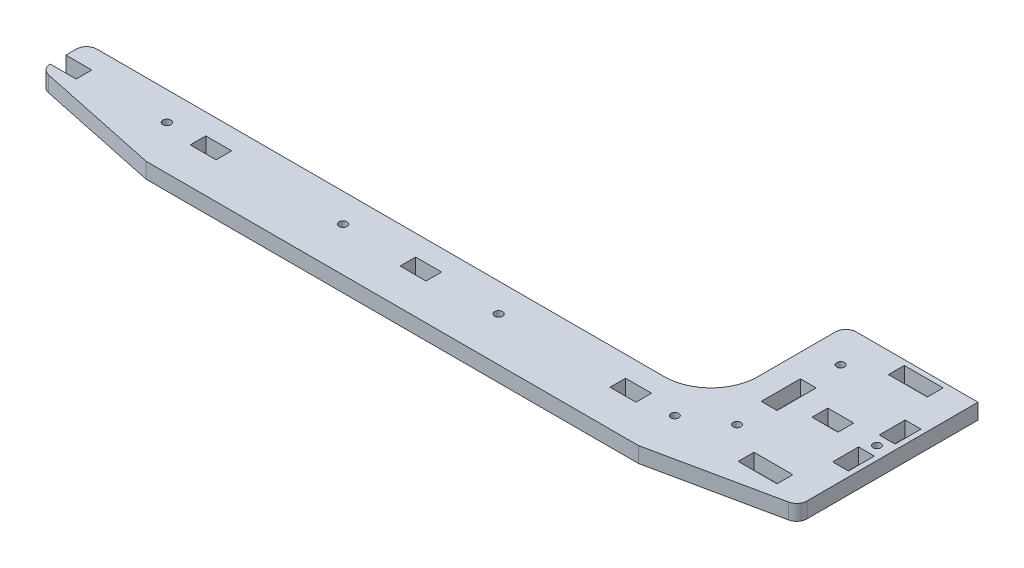
SolidWorks part; units mm, degrees
ref_plane "Спереди" through (0, 0, 0) normal (0, 0, 1) x (1, 0, 0)
ref_plane "Сверху" through (0, 0, 0) normal (0, 1, 0) x (1, 0, 0)
ref_plane "Справа" through (0, 0, 0) normal (1, 0, 0) x (0, 0, -1)
sketch "Эскиз1" plane through (0, 0, 0) normal (0, 1, 0) x (1, 0, 0)
  line L0 (105.2165, 20.9384) -> (111.3165, 20.9384)
  line L1 (111.3165, 20.9384) -> (111.3165, 30.9384)
  line L2 (111.3165, 30.9384) -> (105.2165, 30.9384)
  line L3 (105.2165, 30.9384) -> (105.2165, 20.9384)
  line L4 (71.2165, 9.3884) -> (77.3165, 9.3884)
  line L5 (77.3165, 9.3884) -> (77.3165, 24.4884)
  line L6 (77.3165, 24.4884) -> (71.2165, 24.4884)
  line L7 (71.2165, 24.4884) -> (71.2165, 9.3884)
  line L8 (96.3165, 19.9884) -> (86.3165, 19.9884)
  line L9 (86.3165, 19.9884) -> (86.3165, 13.8884)
  line L10 (86.3165, 13.8884) -> (96.3165, 13.8884)
  line L11 (96.3165, 13.8884) -> (96.3165, 19.9884)
  line L12 (111.3165, 2.9384) -> (111.3165, 12.9384)
  line L13 (111.3165, 12.9384) -> (105.2165, 12.9384)
  line L14 (105.2165, 12.9384) -> (105.2165, 2.9384)
  line L15 (105.2165, 2.9384) -> (111.3165, 2.9384)
  line L16 (101.8165, 48.9884) -> (86.8165, 48.9884)
  line L17 (86.8165, 48.9884) -> (86.8165, 42.8884)
  line L18 (86.8165, 42.8884) -> (101.8165, 42.8884)
  line L19 (101.8165, 42.8884) -> (101.8165, 48.9884)
  line L20 (86.8165, -15.1116) -> (101.8165, -15.1116)
  line L21 (101.8165, -15.1116) -> (101.8165, -9.0116)
  line L22 (101.8165, -9.0116) -> (86.8165, -9.0116)
  line L23 (86.8165, -9.0116) -> (86.8165, -15.1116)
  line L24 (-178.6835, -15.0616) -> (-168.6835, -15.0616)
  line L25 (-168.6835, -15.0616) -> (-168.6835, -9.0616)
  line L26 (-168.6835, -9.0616) -> (-178.6835, -9.0616)
  line L27 (-124.6835, -15.0616) -> (-114.6835, -15.0616)
  line L28 (-114.6835, -15.0616) -> (-114.6835, -9.0616)
  line L29 (-114.6835, -9.0616) -> (-124.6835, -9.0616)
  line L30 (-124.6835, -9.0616) -> (-124.6835, -15.0616)
  line L31 (-43.6835, -15.0616) -> (-33.6835, -15.0616)
  line L32 (-33.6835, -15.0616) -> (-33.6835, -9.0616)
  line L33 (-33.6835, -9.0616) -> (-43.6835, -9.0616)
  line L34 (-43.6835, -9.0616) -> (-43.6835, -15.0616)
  line L35 (37.3165, -15.0616) -> (47.3165, -15.0616)
  line L36 (47.3165, -15.0616) -> (47.3165, -9.0616)
  line L37 (47.3165, -9.0616) -> (37.3165, -9.0616)
  line L38 (37.3165, -9.0616) -> (37.3165, -15.0616)
  line L39 (-178.6835, -5.0616) -> (-178.6835, -9.0616)
  line L40 (44.3165, -1.0616) -> (-174.6835, -1.0616)
  line L41 (62.3165, 46.9384) -> (62.3165, 16.9384)
  line L42 (113.3165, 50.9384) -> (66.3165, 50.9384)
  line L43 (113.3165, -15.0616) -> (113.3165, 50.9384)
  line L44 (-175.5089, -18.9755) -> (-127.6835, -29.0616)
  line L45 (-127.6835, -29.0616) -> (62.3165, -29.0616)
  line L46 (62.3165, -29.0616) -> (110.1419, -18.9755)
  circle A0 centre (59.3165, -12.0616) radius 1.5
  circle A1 centre (74.3165, -3.0616) radius 1.5
  circle A2 centre (108.3165, 16.9384) radius 1.5
  circle A3 centre (74.3165, 36.9384) radius 1.5
  arc A4 (-174.6835, -1.0616) -> (-178.6835, -5.0616) centre (-174.6835, -5.0616) ccw
  arc A5 (66.3165, 50.9384) -> (62.3165, 46.9384) centre (66.3165, 46.9384) ccw
  arc A6 (109.3165, -19.0616) -> (113.3165, -15.0616) centre (109.3165, -15.0616) ccw
  arc A7 (-178.6835, -15.0616) -> (-174.6835, -19.0616) centre (-174.6835, -15.0616) ccw
  circle A8 centre (-136.6835, -12.0616) radius 1.55
  circle A9 centre (-68.6835, -12.0616) radius 1.55
  circle A10 centre (-8.6835, -12.0616) radius 1.55
  arc A11 (44.3165, -1.0616) -> (62.3165, 16.9384) centre (44.3165, 16.9384) ccw
extrude "Бобышка-Вытянуть1" add sketch "Эскиз1" along normal blind 6
